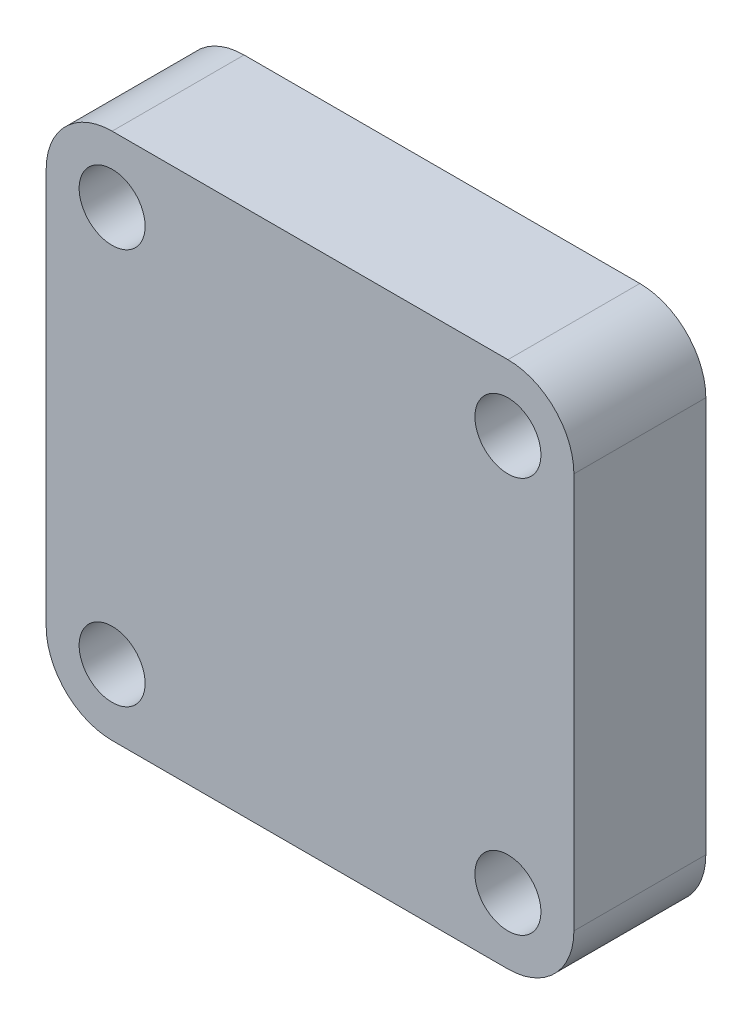
SolidWorks part; units mm, degrees
ref_plane "Front Plane" through (0, 0, 0) normal (0, 0, 1) x (1, 0, 0)
ref_plane "Top Plane" through (0, 0, 0) normal (0, 1, 0) x (1, 0, 0)
ref_plane "Right Plane" through (0, 0, 0) normal (1, 0, 0) x (0, 0, -1)
sketch "Sketch1" plane through (0, 0, 0) normal (0, 0, 1) x (1, 0, 0)
  line L1 (0, 0) -> (40, 0)
  line L2 (0, 0) -> (0, 40)
  line L3 (0, 40) -> (40, 40)
  line L4 (40, 0) -> (40, 40)
  dimension "D1" = 40
  dimension "D2" = 40
extrude "Boss-Extrude1" add sketch "Sketch1" along normal blind 10
sketch "Sketch2" plane through (0, 0, 10) normal (0, 0, 1) x (1, 0, 0)
  line L0 (0, 40) -> (0, 0) construction
  line L2 (40, 40) -> (0, 40) construction
  circle A0 centre (5, 35) radius 2.5
  dimension "D1" = 5
  dimension "D2" = 5
extrude "Cut-Extrude1" cut sketch "Sketch2" against normal through all
ref_plane "Plane1" through (0, 20, 0) normal (0, 1, 0) x (1, 0, 0)
mirror "Mirror1" about plane through (0, 20, 0) normal (0, 1, 0) of "Cut-Extrude1"
ref_plane "Plane2" through (20, 0, 0) normal (1, 0, 0) x (0, 0, -1)
mirror "Mirror2" about plane through (20, 0, 0) normal (1, 0, 0) of "Mirror1", "Cut-Extrude1"
fillet "Fillet2" radius 5 4 edges at (40, 40, 5) (40, 0, 5) (0, 0, 5) (0, 40, 5)
